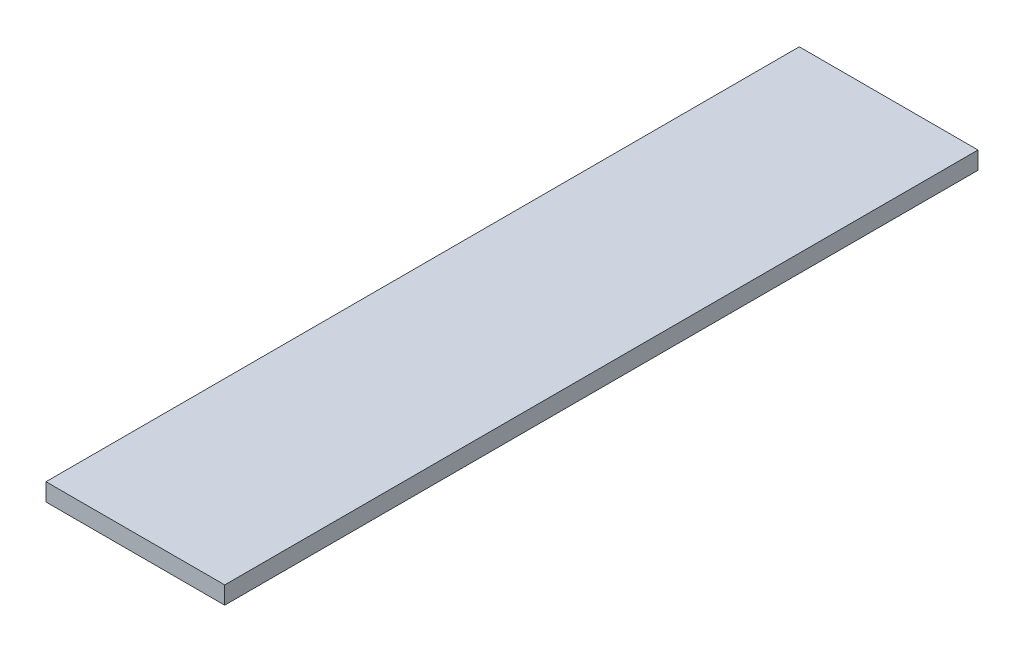
SolidWorks part; units mm, degrees
ref_plane "Front Plane" through (0, 0, 0) normal (0, 0, 1) x (1, 0, 0)
ref_plane "Top Plane" through (0, 0, 0) normal (0, 1, 0) x (1, 0, 0)
ref_plane "Right Plane" through (0, 0, 0) normal (1, 0, 0) x (0, 0, -1)
sketch "Sketch1" plane through (0, 0, 0) normal (0, 0, 1) x (1, 0, 0)
  line L1 (-25.4, 2.5) -> (25.4, 2.5)
  line L2 (-25.4, 2.5) -> (-25.4, -2.5)
  line L3 (-25.4, -2.5) -> (25.4, -2.5)
  line L4 (25.4, 2.5) -> (25.4, -2.5)
  line L5 (-25.4, 2.5) -> (25.4, -2.5) construction
  line L6 (-25.4, -2.5) -> (25.4, 2.5) construction
  point P0 (0, 0)
  dimension "D1" = 5
  dimension "D2" = 50.8
extrude "Boss-Extrude1" add sketch "Sketch1" along normal blind 214.122
